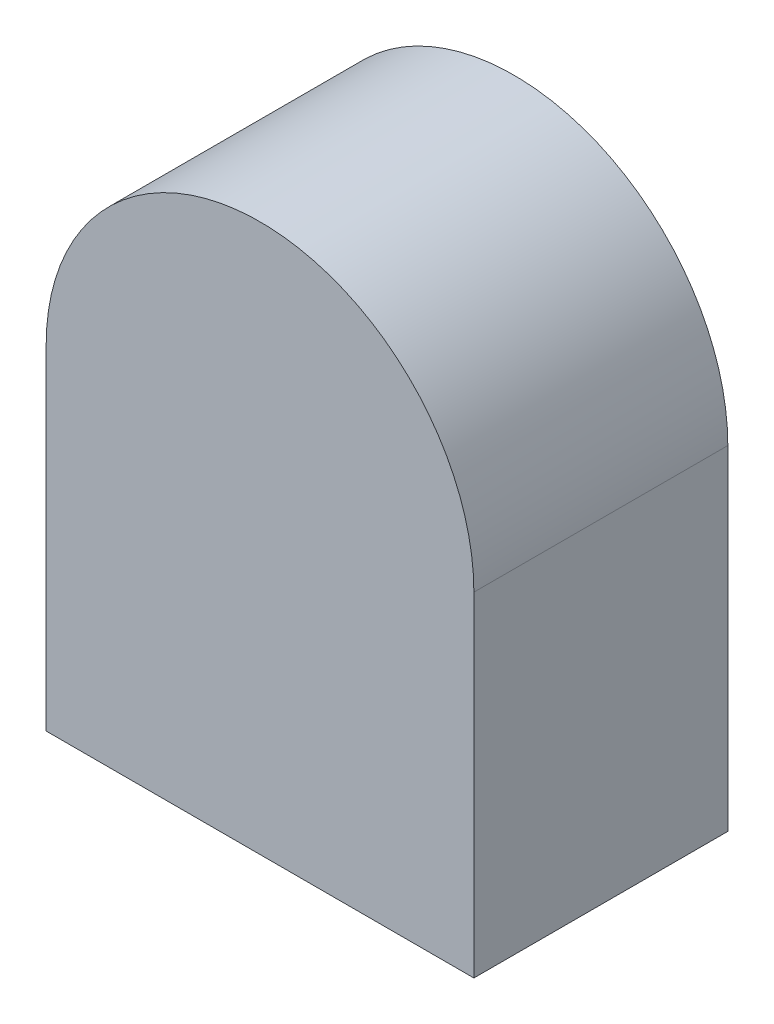
SolidWorks part; units mm, degrees
other "攝影機1"
material "ABS"
ref_plane "前基準面" through (0, 0, 0) normal (0, 0, 1) x (1, 0, 0)
ref_plane "上基準面" through (0, 0, 0) normal (0, 1, 0) x (1, 0, 0)
ref_plane "右基準面" through (0, 0, 0) normal (1, 0, 0) x (0, 0, -1)
sketch "草圖1" plane through (0, 0, 0) normal (0, 0, 1) x (1, 0, 0)
  line L0 (-16, 0) -> (-16, -25)
  line L1 (-16, -25) -> (16, -25)
  line L2 (16, -25) -> (16, 0)
  arc A0 (-16, 0) -> (16, 0) centre (0, 0) cw
  point P4 (0, 16)
  dimension "D1" = 16
  dimension "D2" = 32
  dimension "D3" = 41
extrude "填料-伸長1" add sketch "草圖1" along normal blind 19
sketch "草圖2" plane through (0, 0, 0) normal (0, 0, -1) x (-1, 0, 0)
  circle A0 centre (0, 0) radius 5
  dimension "D1" = 10
extrude "除料-伸長1" cut sketch "草圖2" against normal blind 2
sketch "草圖3" plane through (0, 0, 2) normal (0, 0, -1) x (-1, 0, 0)
  circle A0 centre (0, 0) radius 1.5
  dimension "D1" = 3
extrude "除料-伸長2" cut sketch "草圖3" against normal blind 10
